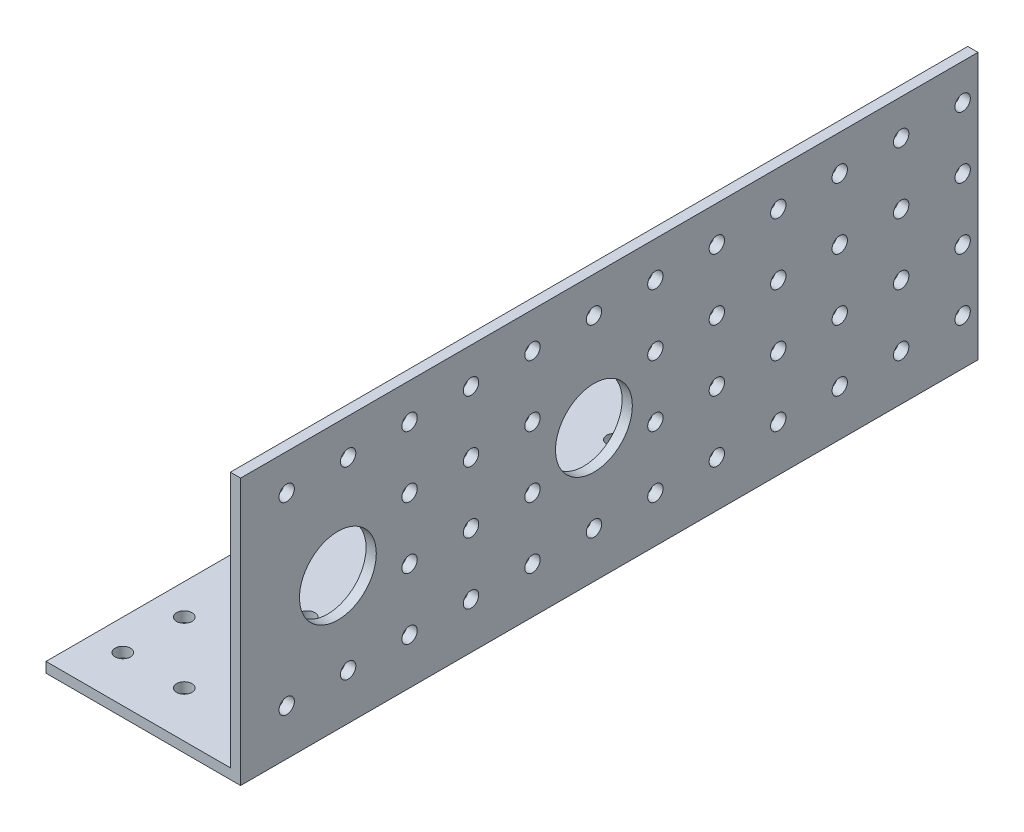
SolidWorks part; units mm, degrees
ref_plane "Front Plane" through (0, 0, 0) normal (0, 0, 1) x (1, 0, 0)
ref_plane "Top Plane" through (0, 0, 0) normal (0, 1, 0) x (1, 0, 0)
ref_plane "Right Plane" through (0, 0, 0) normal (1, 0, 0) x (0, 0, -1)
sketch "Sketch1" plane through (0, 0, 0) normal (0, 1, 0) x (1, 0, 0)
  line L1 (0, 0) -> (38, 0)
  line L2 (0, 0) -> (0, -150)
  line L3 (0, -150) -> (38, -150)
  line L4 (38, 0) -> (38, -150)
  circle A0 centre (6, -3) radius 1.5
  circle A1 centre (18, -3) radius 1.5
  circle A2 centre (30, -3) radius 1.5
  circle A7 centre (18, -15) radius 1.5
  circle A8 centre (30, -15) radius 1.5
  circle A13 centre (18, -27) radius 1.5
  circle A14 centre (30, -27) radius 1.5
  circle A19 centre (18, -39) radius 1.5
  circle A20 centre (30, -39) radius 1.5
  circle A25 centre (18, -51) radius 1.5
  circle A26 centre (30, -51) radius 1.5
  circle A31 centre (18, -63) radius 1.5
  circle A32 centre (30, -63) radius 1.5
  circle A37 centre (18, -75) radius 1.5
  circle A38 centre (30, -75) radius 1.5
  circle A43 centre (18, -87) radius 1.5
  circle A44 centre (30, -87) radius 1.5
  circle A49 centre (18, -99) radius 1.5
  circle A50 centre (30, -99) radius 1.5
  circle A55 centre (18, -111) radius 1.5
  circle A56 centre (30, -111) radius 1.5
  circle A61 centre (18, -123) radius 1.5
  circle A62 centre (30, -123) radius 1.5
  circle A67 centre (18, -135) radius 1.5
  circle A68 centre (30, -135) radius 1.5
  circle A73 centre (18, -147) radius 1.5
  circle A74 centre (30, -147) radius 1.5
  circle A79 centre (6, -15) radius 1.5
  circle A80 centre (6, -27) radius 1.5
  circle A81 centre (6, -39) radius 1.5
  circle A82 centre (6, -51) radius 1.5
  circle A83 centre (6, -63) radius 1.5
  circle A84 centre (6, -75) radius 1.5
  circle A85 centre (6, -87) radius 1.5
  circle A86 centre (6, -99) radius 1.5
  circle A87 centre (6, -111) radius 1.5
  circle A88 centre (6, -123) radius 1.5
  circle A89 centre (6, -135) radius 1.5
  circle A90 centre (6, -147) radius 1.5
  circle A91 centre (66, -3) radius 1.5 [skipped]
  circle A92 centre (78, -3) radius 1.5 [skipped]
  circle A93 centre (66, -15) radius 1.5 [skipped]
  circle A94 centre (78, -15) radius 1.5 [skipped]
  circle A95 centre (54, -27) radius 1.5 [skipped]
  circle A96 centre (66, -27) radius 1.5 [skipped]
  circle A97 centre (78, -27) radius 1.5 [skipped]
  circle A98 centre (54, -39) radius 1.5 [skipped]
  circle A99 centre (66, -39) radius 1.5 [skipped]
  circle A100 centre (78, -39) radius 1.5 [skipped]
  circle A101 centre (54, -51) radius 1.5 [skipped]
  circle A102 centre (66, -51) radius 1.5 [skipped]
  circle A103 centre (78, -51) radius 1.5 [skipped]
  circle A104 centre (54, -63) radius 1.5 [skipped]
  circle A105 centre (66, -63) radius 1.5 [skipped]
  circle A106 centre (78, -63) radius 1.5 [skipped]
  circle A107 centre (54, -75) radius 1.5 [skipped]
  circle A108 centre (66, -75) radius 1.5 [skipped]
  circle A109 centre (78, -75) radius 1.5 [skipped]
  circle A110 centre (54, -87) radius 1.5 [skipped]
  circle A111 centre (66, -87) radius 1.5 [skipped]
  circle A112 centre (78, -87) radius 1.5 [skipped]
  circle A113 centre (54, -99) radius 1.5 [skipped]
  circle A114 centre (66, -99) radius 1.5 [skipped]
  circle A115 centre (78, -99) radius 1.5 [skipped]
  circle A116 centre (54, -111) radius 1.5 [skipped]
  circle A117 centre (66, -111) radius 1.5 [skipped]
  circle A118 centre (78, -111) radius 1.5 [skipped]
  circle A119 centre (54, -123) radius 1.5 [skipped]
  circle A120 centre (66, -123) radius 1.5 [skipped]
  circle A121 centre (78, -123) radius 1.5 [skipped]
  circle A122 centre (54, -135) radius 1.5 [skipped]
  circle A123 centre (66, -135) radius 1.5 [skipped]
  circle A124 centre (78, -135) radius 1.5 [skipped]
  circle A125 centre (54, -147) radius 1.5 [skipped]
  circle A126 centre (66, -147) radius 1.5 [skipped]
  circle A127 centre (54, -3) radius 1.5 [skipped]
  circle A128 centre (54, -15) radius 1.5 [skipped]
  circle A129 centre (78, -147) radius 1.5 [skipped]
  circle A130 centre (42, -3) radius 1.5 [skipped]
  circle A131 centre (42, -15) radius 1.5 [skipped]
  circle A132 centre (42, -27) radius 1.5 [skipped]
  circle A133 centre (42, -39) radius 1.5 [skipped]
  circle A134 centre (42, -51) radius 1.5 [skipped]
  circle A135 centre (42, -63) radius 1.5 [skipped]
  circle A136 centre (42, -75) radius 1.5 [skipped]
  circle A137 centre (42, -87) radius 1.5 [skipped]
  circle A138 centre (42, -99) radius 1.5 [skipped]
  circle A139 centre (42, -111) radius 1.5 [skipped]
  circle A140 centre (42, -123) radius 1.5 [skipped]
  circle A141 centre (42, -135) radius 1.5 [skipped]
  circle A142 centre (42, -147) radius 1.5 [skipped]
  dimension "D3" = 3
  dimension "D4" = 3
  dimension "D5" = 6
  dimension "D8" = 12
  dimension "D9" = 15
  dimension "D1" = 38
  dimension "D2" = 150
  dimension "D6" = 7
  dimension "D7" = 13
extrude "Boss-Extrude1" add sketch "Sketch1" along normal blind 2
sketch "Sketch2" plane through (0, 2, 0) normal (0, 1, 0) x (1, 0, 0)
  line L0 (38, 0) -> (0, 0) construction
  line L1 (38, -150) -> (36, -150)
  line L2 (38, -150) -> (38, 0)
  line L3 (38, 0) -> (36, 0)
  line L4 (36, -150) -> (36, 0)
  dimension "D1" = 2
extrude "Boss-Extrude2" add sketch "Sketch2" along normal blind 50
sketch "Sketch3" plane through (38, 0, 0) normal (1, 0, 0) x (0, 0, -1)
  line L0 (-150, 52) -> (0, 52) construction
  line L1 (-150, 52) -> (-150, 0) construction
  line L2 (-75, 26) -> (-125, 26) construction
  line L3 (-75, 26) -> (-75, 52) construction
  line L5 (-150, 0) -> (0, 0) construction
  circle A0 centre (-147, 45) radius 1.5
  circle A1 centre (-135, 45) radius 1.5
  circle A2 centre (-123, 45) radius 1.5
  circle A3 centre (-111, 45) radius 1.5
  circle A4 centre (-99, 45) radius 1.5
  circle A5 centre (-87, 45) radius 1.5
  circle A6 centre (-75, 45) radius 1.5
  circle A7 centre (-63, 45) radius 1.5
  circle A8 centre (-51, 45) radius 1.5
  circle A9 centre (-39, 45) radius 1.5
  circle A10 centre (-27, 45) radius 1.5
  circle A11 centre (-15, 45) radius 1.5
  circle A12 centre (-3, 45) radius 1.5
  circle A15 centre (-111, 33) radius 1.5
  circle A16 centre (-99, 33) radius 1.5
  circle A17 centre (-87, 33) radius 1.5
  circle A19 centre (-63, 33) radius 1.5
  circle A20 centre (-51, 33) radius 1.5
  circle A21 centre (-39, 33) radius 1.5
  circle A22 centre (-27, 33) radius 1.5
  circle A24 centre (-3, 33) radius 1.5
  circle A27 centre (-111, 21) radius 1.5
  circle A28 centre (-99, 21) radius 1.5
  circle A29 centre (-87, 21) radius 1.5
  circle A31 centre (-63, 21) radius 1.5
  circle A32 centre (-51, 21) radius 1.5
  circle A33 centre (-39, 21) radius 1.5
  circle A34 centre (-27, 21) radius 1.5
  circle A36 centre (-3, 21) radius 1.5
  circle A37 centre (-135, 9) radius 1.5
  circle A38 centre (-123, 9) radius 1.5
  circle A39 centre (-111, 9) radius 1.5
  circle A40 centre (-99, 9) radius 1.5
  circle A41 centre (-87, 9) radius 1.5
  circle A42 centre (-75, 9) radius 1.5
  circle A43 centre (-63, 9) radius 1.5
  circle A44 centre (-51, 9) radius 1.5
  circle A45 centre (-39, 9) radius 1.5
  circle A46 centre (-27, 9) radius 1.5
  circle A47 centre (-15, 9) radius 1.5
  circle A48 centre (-3, 9) radius 1.5
  circle A61 centre (-147, 33) radius 1.5
  circle A62 centre (-147, 21) radius 1.5
  circle A63 centre (-147, 9) radius 1.5
  circle A65 centre (-135, -3) radius 1.5 [skipped]
  circle A66 centre (-123, -3) radius 1.5 [skipped]
  circle A67 centre (-111, -3) radius 1.5 [skipped]
  circle A68 centre (-99, -3) radius 1.5 [skipped]
  circle A69 centre (-87, -3) radius 1.5 [skipped]
  circle A70 centre (-75, -3) radius 1.5 [skipped]
  circle A71 centre (-63, -3) radius 1.5 [skipped]
  circle A72 centre (-51, -3) radius 1.5 [skipped]
  circle A73 centre (-39, -3) radius 1.5 [skipped]
  circle A74 centre (-27, -3) radius 1.5 [skipped]
  circle A75 centre (-15, -3) radius 1.5 [skipped]
  circle A76 centre (-3, -3) radius 1.5 [skipped]
  circle A77 centre (-147, -3) radius 1.5 [skipped]
  circle A78 centre (-75, 26) radius 7.5
  circle A79 centre (-75, 21) radius 1.5 [skipped]
  circle A80 centre (-75, 33) radius 1.5 [skipped]
  circle A83 centre (-15, 21) radius 1.5 [skipped]
  circle A84 centre (-15, 33) radius 1.5 [skipped]
  circle A86 centre (-135, 21) radius 1.5 [skipped]
  circle A87 centre (-135, 33) radius 1.5 [skipped]
  circle A90 centre (-15, 21) radius 1.5
  circle A91 centre (-15, 33) radius 1.5
  circle A92 centre (-125, 26) radius 7.5
  circle A93 centre (-123, 33) radius 1.5 [skipped]
  circle A94 centre (-123, 21) radius 1.5 [skipped]
  dimension "D1" = 7
  dimension "D2" = 3
  dimension "D3" = 3
  dimension "D6" = 12
  dimension "D7" = 12
  dimension "D8" = 15
  dimension "D9" = 26
  dimension "D11" = 2
  dimension "D12" = 15
  dimension "D15" = 15
  dimension "D14" = 50
  dimension "D4" = 13
  dimension "D5" = 5
extrude "Cut-Extrude1" cut sketch "Sketch3" against normal blind 50
sketch "Sketch4" plane through (0, 0, 150) normal (0, 0, 1) x (1, 0, 0)
  line L6 (0, 0) -> (38, 0)
  line L7 (38, 0) -> (38, 52)
  line L8 (38, 52) -> (36, 52)
  line L9 (36, 52) -> (36, 2)
  line L10 (36, 2) -> (0, 2)
  line L11 (0, 2) -> (0, 0)
  line L12 (0, 0) -> (38, 0)
  line L13 (38, 0) -> (38, 52)
  line L14 (38, 52) -> (36, 52)
  line L15 (36, 52) -> (36, 2)
  line L16 (36, 2) -> (0, 2)
  line L17 (0, 2) -> (0, 0)
  dimension "D1" = 0
extrude "Cut-Extrude2" cut sketch "Sketch4" against normal blind 6
